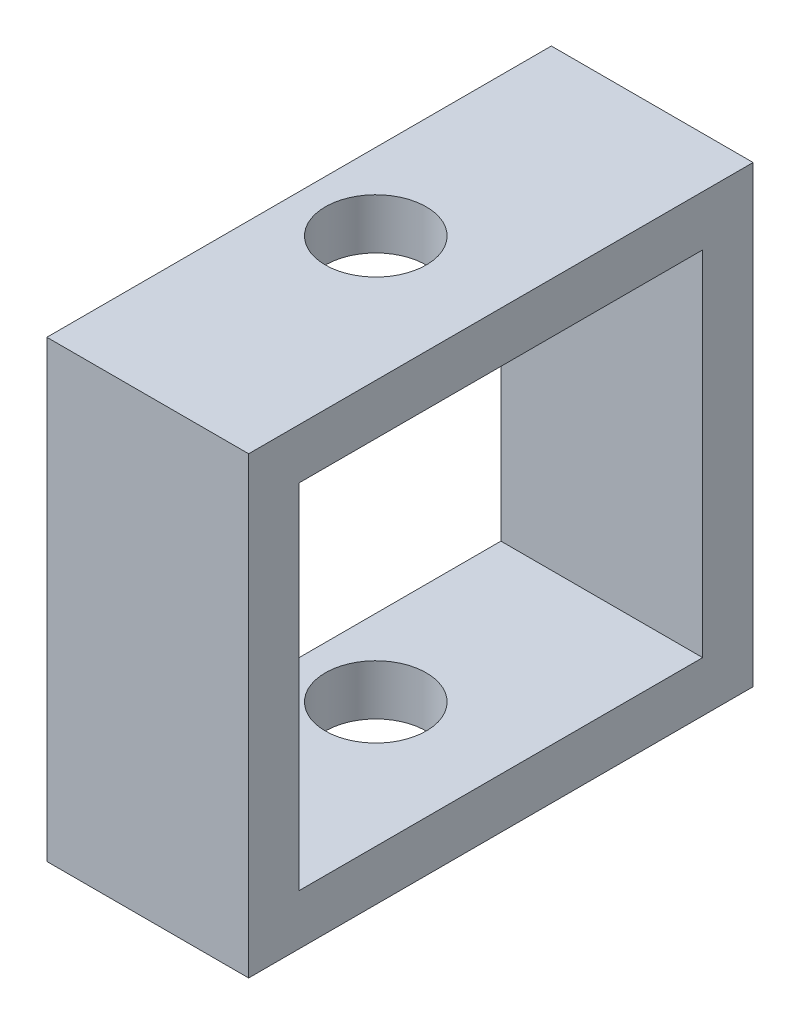
SolidWorks part; units mm, degrees
material "6061-T6 (SS)"
ref_plane "Front Plane" through (0, 0, 0) normal (0, 0, 1) x (1, 0, 0)
ref_plane "Top Plane" through (0, 0, 0) normal (0, 1, 0) x (1, 0, 0)
ref_plane "Right Plane" through (0, 0, 0) normal (1, 0, 0) x (0, 0, -1)
sketch "Sketch1" plane through (0, 0, 0) normal (0, 1, 0) x (1, 0, 0)
  line L1 (0, 0) -> (12.7, 0)
  line L2 (0, 0) -> (0, 31.75)
  line L3 (0, 31.75) -> (12.7, 31.75)
  line L4 (12.7, 0) -> (12.7, 31.75)
  circle A0 centre (4.826, 15.875) radius 3.175
  point P7 (0, 0)
  point P8 (0, 0)
  point P9 (0, 15.875)
  dimension "D1" = 6.35
  dimension "D2" = 31.75
  dimension "D3" = 12.7
  dimension "D5" = 4.826
extrude "Boss-Extrude2" add sketch "Sketch1" along normal blind 3.175
sketch "Sketch2" plane through (0, 3.175, 0) normal (0, 1, 0) x (1, 0, 0)
  line L0 (12.7, 0) -> (12.7, 31.75) construction
  line L1 (0, 31.75) -> (12.7, 31.75)
  line L2 (0, 31.75) -> (0, 28.575)
  line L3 (0, 28.575) -> (12.7, 28.575)
  line L4 (12.7, 31.75) -> (12.7, 28.575)
  line L6 (12.7, 28.575) -> (11.684, 28.575)
  line L7 (12.7, 28.575) -> (12.7, 0)
  line L15 (0, 3.175) -> (12.7, 3.175)
  line L16 (0, 31.75) -> (0, 0) construction
  line L17 (0, 0) -> (12.7, 0) construction
  line M9 (0, 31.75) -> (0, 0)
  line M10 (0, 0) -> (12.7, 0)
  line M11 (12.7, 0) -> (12.7, 31.75)
  line M12 (12.7, 31.75) -> (0, 31.75)
  dimension "D1" = 3.175
  dimension "D3" = 3.175
extrude "Boss-Extrude4" add sketch "Sketch2" along normal blind 22.225 contours L3 M9 M11 M12 | L15 M9 M10 M11
sketch "Sketch3" plane through (0, 25.4, 0) normal (0, 1, 0) x (1, 0, 0)
  line L0 (12.7, 28.575) -> (12.7, 31.75) construction
  line L1 (12.7, 3.175) -> (12.7, 28.575) construction
  line L2 (12.7, 0) -> (12.7, 3.175) construction
  line L3 (0, 0) -> (12.7, 0) construction
  line L4 (0, 3.175) -> (0, 0) construction
  line L5 (0, 31.75) -> (0, 28.575) construction
  line L6 (0, 28.575) -> (0, 3.175) construction
  line L7 (12.7, 31.75) -> (0, 31.75) construction
  line L8 (12.7, 28.575) -> (12.7, 31.75)
  line L9 (12.7, 3.175) -> (12.7, 28.575)
  line L10 (12.7, 0) -> (12.7, 3.175)
  line L11 (0, 0) -> (12.7, 0)
  line L12 (0, 3.175) -> (0, 0)
  line L13 (0, 31.75) -> (0, 28.575)
  line L14 (0, 28.575) -> (0, 3.175)
  line L15 (12.7, 31.75) -> (0, 31.75)
  circle A1 centre (4.826, 15.875) radius 3.175
  point P0 (0, 0)
  point P1 (0, 15.875)
  point P7 (4.826, 22.225)
extrude "Boss-Extrude5" add sketch "Sketch3" along normal blind 3.175
